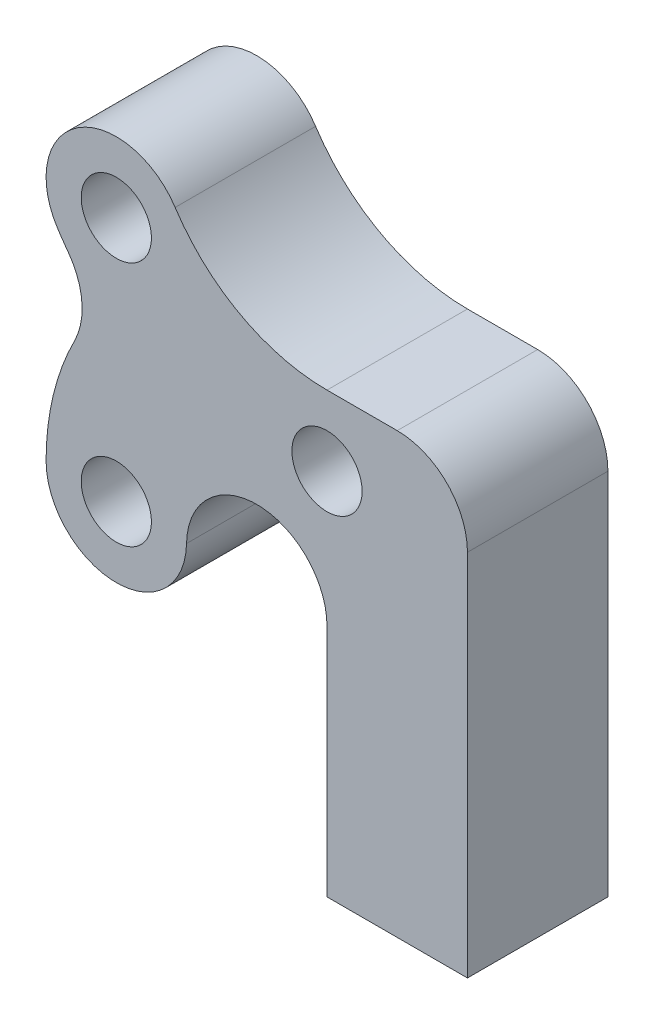
SolidWorks part; units mm, degrees
ref_plane "Plan de face" through (0, 0, 0) normal (0, 0, 1) x (1, 0, 0)
ref_plane "Plan de dessus" through (0, 0, 0) normal (0, 1, 0) x (1, 0, 0)
ref_plane "Plan de droite" through (0, 0, 0) normal (1, 0, 0) x (0, 0, -1)
sketch "Esquisse1" plane through (0, 0, 0) normal (0, 0, 1) x (1, 0, 0)
  line L0 (-5.1763, 4.7706) -> (-5.1763, -3.2294) construction
  line L1 (14.8237, -22.7294) -> (6.8237, -22.7294)
  line L2 (14.8237, -22.7294) -> (14.8237, 2.2706)
  line L3 (14.8237, 2.2706) -> (6.8237, 2.2706)
  line L4 (6.8237, -22.7294) -> (6.8237, 2.2706) construction
  line L5 (-5.1763, -3.2294) -> (6.8237, -3.2294) construction
  line L6 (-5.1763, -3.2294) -> (-5.1763, -9.2294) construction
  line L7 (6.8237, -3.2294) -> (6.8237, -1.7294) construction
  line L8 (-8.5267, 2.5854) -> (-1.826, 6.9559) construction
  line L9 (-9.1763, -9.2294) -> (-1.1763, -9.2294) construction
  line L10 (6.8237, -5.7294) -> (6.8237, -22.7294)
  circle A0 centre (-5.1763, 4.7706) radius 6.5 construction
  circle A5 centre (6.8237, -1.7294) radius 6.5 construction
  circle A10 centre (-5.1763, -9.2294) radius 6.5 construction
  arc A11 (-5.1763, 4.7706) -> (6.8237, -1.7294) centre (6.8237, 12.5975) ccw construction
  arc A12 (-8.5267, 2.5854) -> (6.8237, -5.7294) centre (6.8237, 12.5975) ccw construction
  arc A13 (-1.826, 6.9559) -> (6.8237, 2.2706) centre (6.8237, 12.5975) ccw construction
  arc A14 (-1.826, 6.9559) -> (-8.5267, 2.5854) centre (-5.1763, 4.7706) ccw construction
  arc A15 (6.8237, -5.7294) -> (6.8237, 2.2706) centre (6.8237, -1.7294) ccw construction
  arc A16 (0, 0) -> (-5.1763, -9.2294) centre (5.6398, -9.2294) ccw construction
  arc A17 (-2.0857, 3.4132) -> (-9.1763, -9.2294) centre (5.6398, -9.2294) ccw construction
  arc A18 (2.0857, -3.4132) -> (-1.1763, -9.2294) centre (5.6398, -9.2294) ccw construction
  arc A19 (2.0857, -3.4132) -> (-2.0857, 3.4132) centre (0, 0) ccw construction
  arc A20 (-9.1763, -9.2294) -> (-1.1763, -9.2294) centre (-5.1763, -9.2294) ccw construction
  circle A21 centre (-5.1763, 4.7706) radius 2
  circle A22 centre (6.8237, -1.7294) radius 2
  circle A23 centre (-5.1763, -9.2294) radius 2
  arc A24 (-1.826, 6.9559) -> (-8.5267, 2.5854) centre (-5.1763, 4.7706) ccw
  arc A25 (-1.826, 6.9559) -> (6.8237, 2.2706) centre (6.8237, 12.5975) ccw
  arc A26 (-8.5267, 2.5854) -> (-6.189, -0.3077) centre (6.8237, 12.5975) ccw
  arc A27 (-6.189, -0.3077) -> (-9.1763, -9.2294) centre (5.6398, -9.2294) ccw
  arc A28 (-9.1763, -9.2294) -> (-1.1763, -9.2294) centre (-5.1763, -9.2294) ccw
  arc A29 (-1.1763, -9.2294) -> (0.6, -4.6403) centre (5.6398, -9.2294) cw
  arc A30 (0.6, -4.6403) -> (6.8237, -5.7294) centre (6.8237, 12.5975) ccw
  point P13 (0, 0)
  point P20 (-3.7939, -3.9384)
  dimension "D3" = 8
  dimension "D1" = 13
  dimension "D6" = 4
  dimension "D2" = 1.5
  dimension "D4" = 12
  dimension "D5" = 14
  dimension "D7" = 8
  dimension "D8" = 25
  dimension "D9" = 6
extrude "Boss.-Extru.1" add sketch "Esquisse1" along normal blind 8
sketch "Esquisse2" plane through (0, -22.7294, 0) normal (0, -1, 0) x (1, 0, 0)
  line L0 (6.8237, 8) -> (14.8237, 0) construction
  circle A0 centre (10.8237, 4) radius 2
  dimension "D1" = 4
extrude "Enlèv. mat.-Extru.1" cut sketch "Esquisse2" against normal blind 20
fillet "Congé1" radius 4 4 edges at (-6.189, -0.3077, 4) (0.6, -4.6403, 4) (6.8237, -5.7294, 4) (14.8237, 2.2706, 4)
